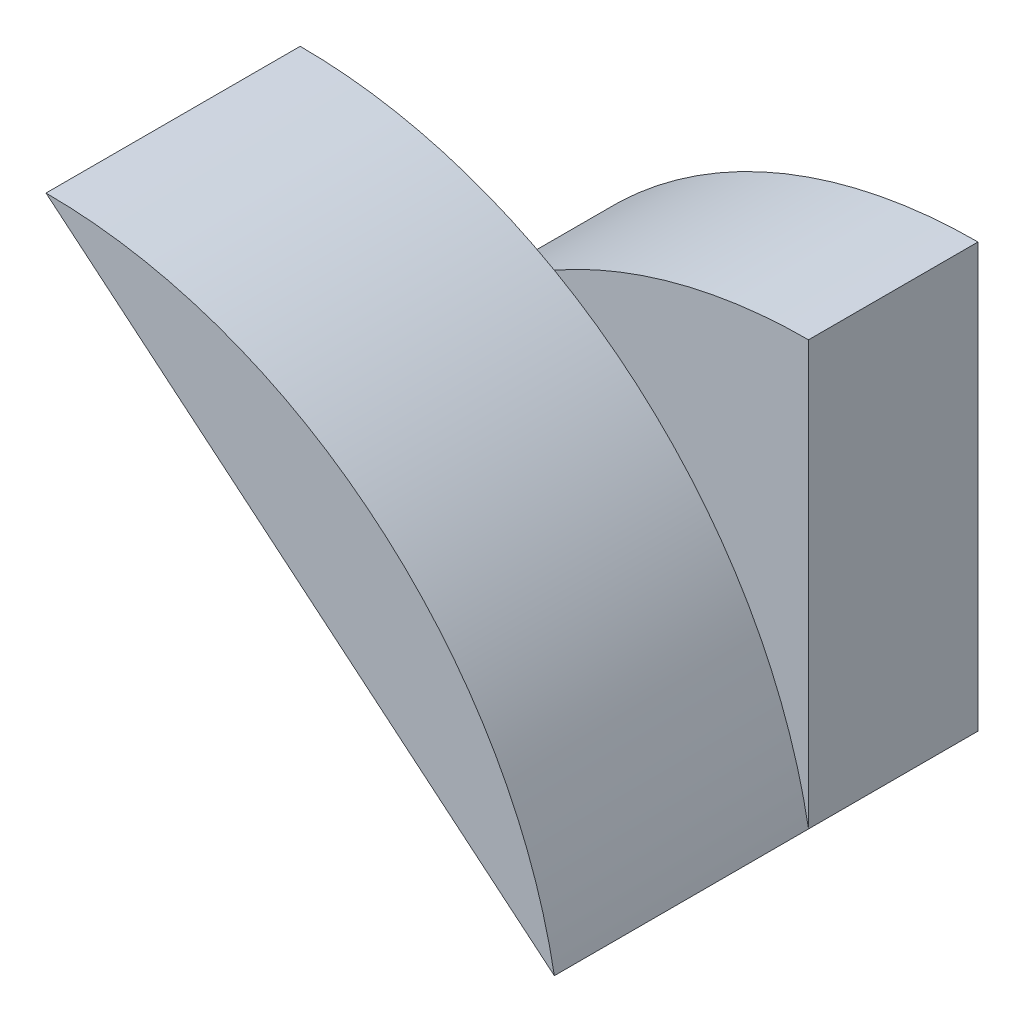
SolidWorks part; units mm, degrees
ref_plane "Front Plane" through (0, 0, 0) normal (0, 0, 1) x (1, 0, 0)
ref_plane "Top Plane" through (0, 0, 0) normal (0, 1, 0) x (1, 0, 0)
ref_plane "Right Plane" through (0, 0, 0) normal (1, 0, 0) x (0, 0, -1)
sketch "Sketch1" plane through (0, 0, 0) normal (0, 0, 1) x (1, 0, 0)
  line L0 (-30, 0) -> (0, 0)
  line L1 (0, 0) -> (0, 25)
  arc A0 (-30, 0) -> (0, 25) centre (0, -5.5) cw
  dimension "D2" = 25
  dimension "D1" = 30
extrude "Boss-Extrude1" add sketch "Sketch1" along normal blind 10
sketch "Sketch2" plane through (0, 0, 10) normal (0, 0, 1) x (1, 0, 0)
  line L0 (-30, 25) -> (0, 0)
  arc A0 (0, 0) -> (-30, 25) centre (-30, -5.5) ccw
  dimension "D1" = 30
  dimension "D2" = 25
extrude "Boss-Extrude2" add sketch "Sketch2" along normal blind 15
